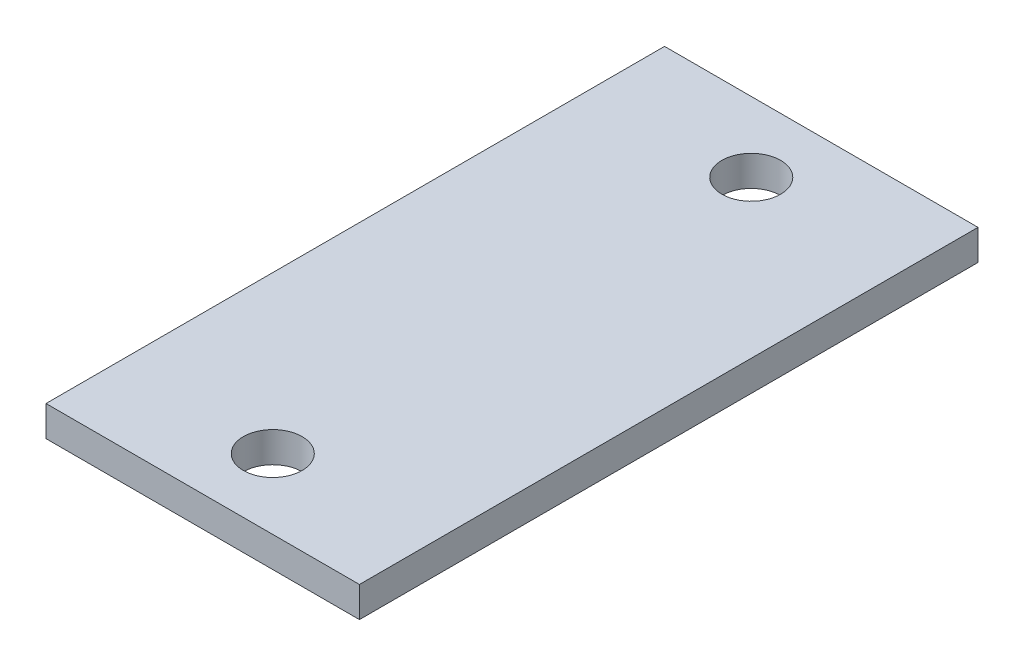
SolidWorks part; units mm, degrees
material "Plain Carbon Steel"
ref_plane "Front Plane" through (0, 0, 0) normal (0, 0, 1) x (1, 0, 0)
ref_plane "Top Plane" through (0, 0, 0) normal (0, 1, 0) x (1, 0, 0)
ref_plane "Right Plane" through (0, 0, 0) normal (1, 0, 0) x (0, 0, -1)
sketch "Sketch1" plane through (0, 0, 0) normal (0, 1, 0) x (1, 0, 0)
  line L1 (0, 0) -> (50.8, 0)
  line L2 (0, 0) -> (0, 100.25)
  line L3 (0, 100.25) -> (50.8, 100.25)
  line L4 (50.8, 0) -> (50.8, 100.25)
  line L8 (0, 11.35) -> (50.8, 11.35) construction
  circle A0 centre (25.4, 11.35) radius 4.7625
  circle A1 centre (25.4, 88.9) radius 4.7625
  dimension "D6" = 9.525
  dimension "D1" = 100.25
  dimension "D2" = 88.9
  dimension "D3" = 25.4
  dimension "D5" = 50.8
  dimension "D7" = 88.9
extrude "Hammer" add sketch "Sketch1" along normal blind 4.9352
